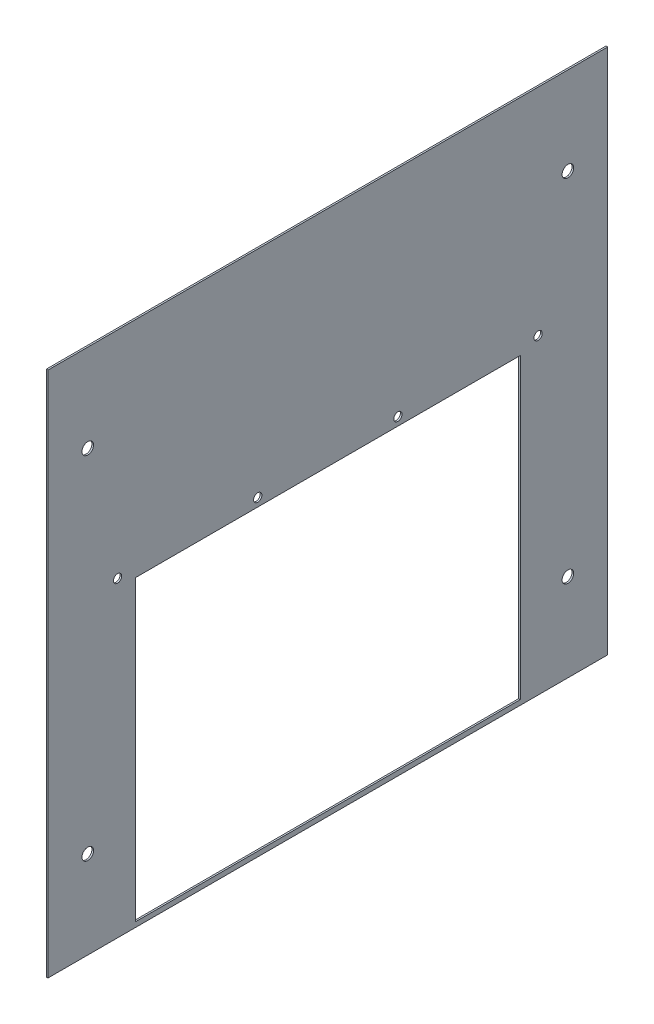
SolidWorks part; units mm, degrees
material "AISI 304"
ref_plane "Front Plane" through (0, 0, 0) normal (0, 0, 1) x (1, 0, 0)
ref_plane "Top Plane" through (0, 0, 0) normal (0, 1, 0) x (1, 0, 0)
ref_plane "Right Plane" through (0, 0, 0) normal (1, 0, 0) x (0, 0, -1)
sketch "Sketch1" plane through (0, 0, 0) normal (1, 0, 0) x (0, 0, -1)
  line L1 (0, 0) -> (338, 0)
  line L2 (0, 0) -> (0, 318)
  line L3 (0, 318) -> (338, 318)
  line L4 (338, 0) -> (338, 318)
  circle A8 centre (24, 265.06) radius 3.5
  circle A9 centre (314, 265.06) radius 3.5
  circle A10 centre (314, 52.94) radius 3.5
  circle A11 centre (24, 52.94) radius 3.5
  dimension "D3" = 7
  dimension "D4" = 24
  dimension "D1" = 318
  dimension "D2" = 338
  dimension "D5" = 24
  dimension "D6" = 52.94
  dimension "D7" = 52.94
extrude "Boss-Extrude1" add sketch "Sketch1" along normal blind 1
sketch "Sketch2" plane through (0, 0, 0) normal (-1, 0, 0) x (0, 0, 1)
  line L0 (-296, 188) -> (-42, 188) construction
  line L1 (-42, 188) -> (-42, 291.2777) construction
  line L2 (-285.25, 183) -> (-52.75, 183)
  line L3 (-338, 318) -> (0, 318) construction
  line L4 (-169, 188) -> (-169, 318) construction
  line L5 (-126.6667, 188) -> (-126.6667, 271.0815) construction
  line L6 (-211.3333, 271.0815) -> (-126.6667, 271.0815) construction
  line L7 (-42, 291.2777) -> (-169, 291.2777) construction
  line L8 (-126.6667, 271.0815) -> (-42, 271.0815) construction
  line L9 (-211.3333, 271.0815) -> (-211.3333, 188) construction
  line L10 (-169, 291.2777) -> (-296, 291.2777) construction
  line L11 (-296, 291.2777) -> (-296, 188) construction
  line L12 (-285.25, 183) -> (-285.25, 3)
  line L13 (-285.25, 3) -> (-52.75, 3)
  line L14 (-52.75, 183) -> (-52.75, 3)
  line L15 (-211.3333, 271.0815) -> (-296, 271.0815) construction
  circle A0 centre (-296, 188) radius 2.5
  circle A1 centre (-211.3333, 188) radius 2.5
  circle A2 centre (-126.6667, 188) radius 2.5
  circle A3 centre (-42, 188) radius 2.5
  point P26 (-169, 183)
  dimension "D2" = 5
  dimension "D6" = 254
  dimension "D1" = 130
  dimension "D3" = 180
  dimension "D4" = 5
  dimension "D5" = 116.25
extrude "Cut-Extrude1" cut sketch "Sketch2" against normal through all
